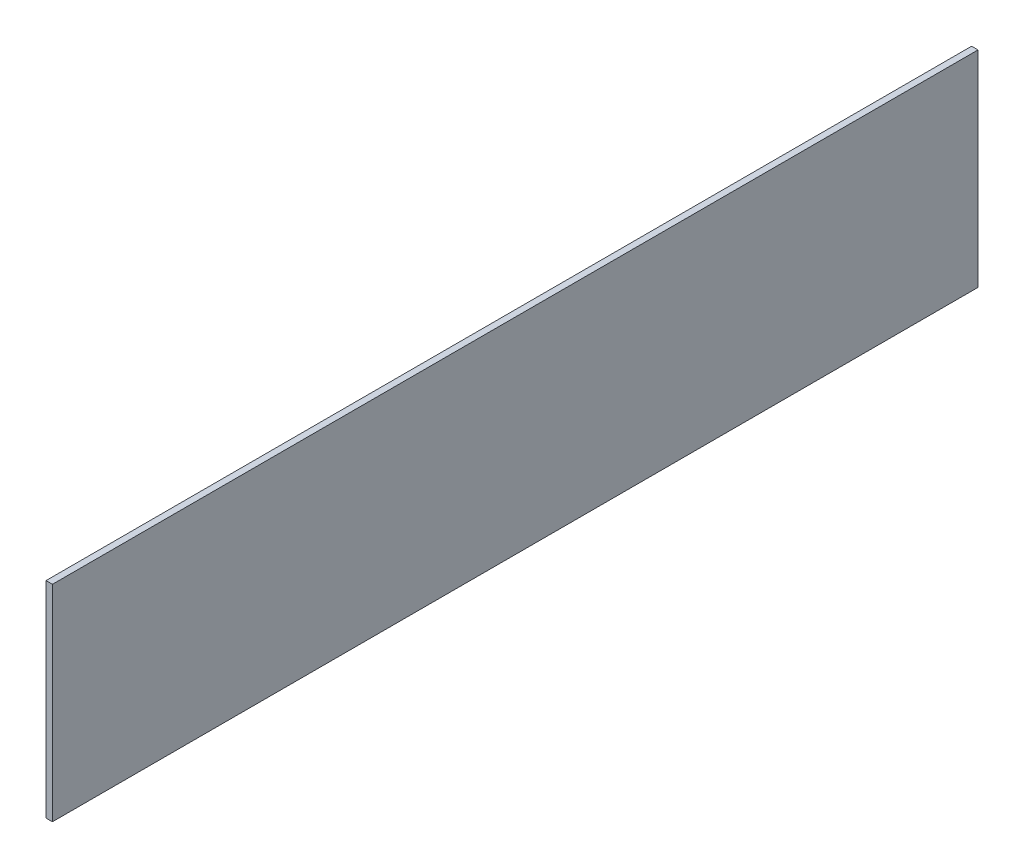
SolidWorks part; units mm, degrees
ref_plane "Front Plane" through (0, 0, 0) normal (0, 0, 1) x (1, 0, 0)
ref_plane "Top Plane" through (0, 0, 0) normal (0, 1, 0) x (1, 0, 0)
ref_plane "Right Plane" through (0, 0, 0) normal (1, 0, 0) x (0, 0, -1)
sketch "Sketch1" plane through (0, 0, 0) normal (1, 0, 0) x (0, 0, -1)
  line L1 (114.3, -25.4) -> (-114.3, -25.4)
  line L2 (114.3, -25.4) -> (114.3, 25.4)
  line L3 (114.3, 25.4) -> (-114.3, 25.4)
  line L4 (-114.3, -25.4) -> (-114.3, 25.4)
  line L5 (114.3, -25.4) -> (-114.3, 25.4) construction
  line L6 (114.3, 25.4) -> (-114.3, -25.4) construction
  point P0 (0, 0)
extrude "Boss-Extrude1" add sketch "Sketch1" along normal mid plane 1.5875
